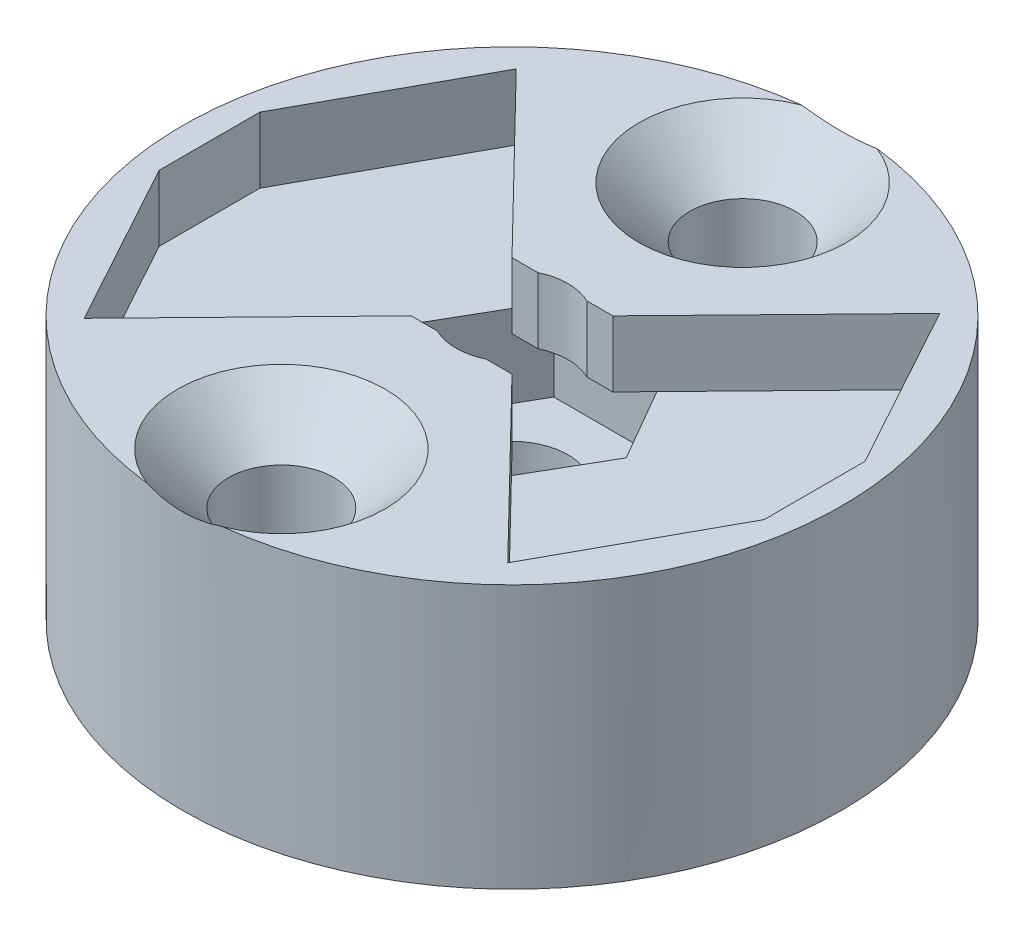
SolidWorks part; units mm, degrees
ref_plane "Płaszczyzna przednia" through (0, 0, 0) normal (0, 0, 1) x (1, 0, 0)
ref_plane "Płaszczyzna górna" through (0, 0, 0) normal (0, 1, 0) x (1, 0, 0)
ref_plane "Płaszczyzna prawa" through (0, 0, 0) normal (1, 0, 0) x (0, 0, -1)
sketch "Sketch1" plane through (0, 0, 0) normal (0, 1, 0) x (1, 0, 0)
  line L0 (0, 7) -> (7, 0) construction
  line L1 (7, 0) -> (0, -7) construction
  line L2 (0, -7) -> (-7, 0) construction
  line L3 (-7, 0) -> (0, 7) construction
  circle A0 centre (0, 0) radius 10
extrude "Boss-Extrude1" add sketch "Sketch1" along normal blind 6
sketch "Sketch8" plane through (0, 6, 0) normal (0, 1, 0) x (1, 0, 0)
  line L1 (3.4641, 0) -> (1.7321, 3)
  line L2 (1.7321, 3) -> (-1.7321, 3)
  line L3 (-1.7321, 3) -> (-3.4641, 0)
  line L4 (-3.4641, 0) -> (-1.7321, -3)
  line L5 (-1.7321, -3) -> (1.7321, -3)
  line L6 (1.7321, -3) -> (3.4641, 0)
  circle A0 centre (0, 0) radius 3 construction
extrude "Cut-Extrude4" cut sketch "Sketch8" against normal blind 2.5
sketch "Sketch9" plane through (0, 6, 0) normal (0, 1, 0) x (1, 0, 0)
  circle A0 centre (0, 0) radius 10
extrude "Boss-Extrude2" add sketch "Sketch9" along normal blind 2
sketch "Sketch14" plane through (0, 8, 0) normal (0, 1, 0) x (1, 0, 0)
  point P0 (0, 7)
  point P3 (0, -7)
hole_wizard "CSK for M3 Countersunk Flat Head Screw2" positions "Sketch14" profile "Sketch15" countersink size "M3" standard "ISO" end condition through all
sketch "Sketch15" plane through (0, 8, -7) normal (1, 0, 0) x (0, 0, 1)
  line L0 (0, 0) -> (0, 8)
  line L1 (0, 8) -> (1.6, 8)
  line L2 (1.6, 8) -> (1.6, 1.55)
  line L3 (1.6, 1.55) -> (3.15, 0)
  line L5 (3.15, 0) -> (0, 0)
  line L6 (-1.6, 1.55) -> (-3.15, 0) construction
  line L11 (0, -6.35) -> (0, 107.95) construction
  dimension "Thru Hole Dia." = 3.2
  dimension "Thru Hole Depth" = 8
  dimension "Near C'Sink Dia." = 6.3
  dimension "Near C'Sink Angle" = 90
sketch "Sketch16" plane through (0, 8, 0) normal (0, 1, 0) x (1, 0, 0)
  line L25 (-6.4264, 6.5554) -> (-9.18, 1.53)
  line L41 (-1.5, -1.5) -> (1.5, -1.5) construction
  line L82 (-1.5, -1.5) -> (-1.5, 1.5) construction
  line L83 (-1.5, 1.5) -> (1.5, 1.5) construction
  line L84 (1.5, -1.5) -> (1.5, 1.5) construction
  line L118 (-1.5, -1.5) -> (1.5, 1.5) construction
  line L119 (-1.5, 1.5) -> (1.5, -1.5) construction
  line L120 (-6.3004, -6.4269) -> (6.3004, -6.4269) construction
  line L121 (-6.3004, -6.4269) -> (-6.3004, 6.4269) construction
  line L122 (-6.3004, 6.4269) -> (6.3004, 6.4269) construction
  line L123 (6.3004, -6.4269) -> (6.3004, 6.4269) construction
  line L124 (-6.3004, -6.4269) -> (6.3004, 6.4269) construction
  line L125 (-6.3004, 6.4269) -> (6.3004, -6.4269) construction
  line L126 (-9, -1.5) -> (9, -1.5) construction
  line L127 (-9, -1.5) -> (-9, 1.5) construction
  line L128 (-9, 1.5) -> (9, 1.5) construction
  line L129 (9, -1.5) -> (9, 1.5) construction
  line L130 (-9, -1.5) -> (9, 1.5) construction
  line L131 (-9, 1.5) -> (9, -1.5) construction
  line L132 (-9.18, 1.53) -> (-9.18, -1.53)
  line L133 (-9.18, -1.53) -> (-6.4264, -6.5554)
  line L134 (-6.4264, -6.5554) -> (-1.53, -1.53)
  line L135 (-1.53, -1.53) -> (1.53, -1.53)
  line L136 (1.53, -1.53) -> (6.4264, -6.5554)
  line L137 (6.4264, -6.5554) -> (9.18, -1.53)
  line L138 (9.18, -1.53) -> (9.18, 1.53)
  line L139 (9.18, 1.53) -> (6.4264, 6.5554)
  line L140 (6.4264, 6.5554) -> (1.53, 1.53)
  line L141 (1.53, 1.53) -> (-1.53, 1.53)
  line L142 (-1.53, 1.53) -> (-6.4264, 6.5554)
  point P0 (0, 0)
  point P5 (0, 0)
  point P14 (0, 0)
extrude "Cut-Extrude6" cut sketch "Sketch16" against normal blind 2
sketch "Sketch18" plane through (0, 8, 0) normal (0, 1, 0) x (1, 0, 0)
  circle A0 centre (0, 0) radius 1.7
extrude "Cut-Extrude8" cut sketch "Sketch18" against normal blind 9
